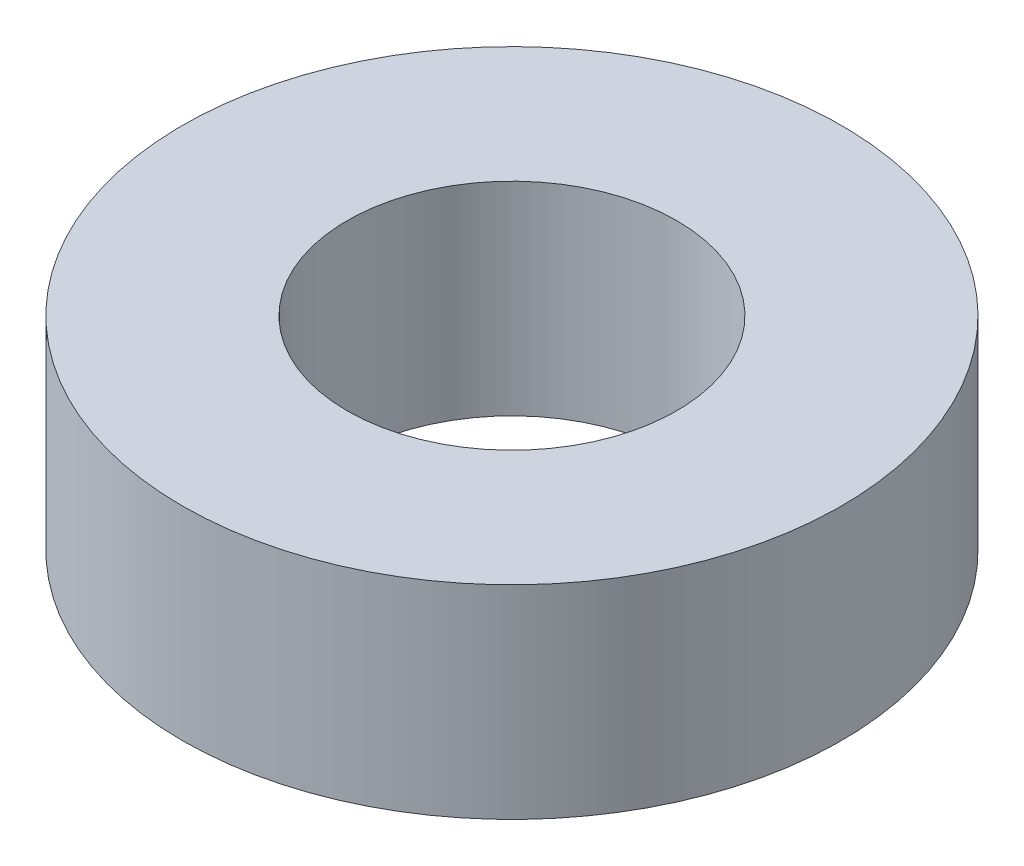
SolidWorks part; units mm, degrees
ref_plane "Front Plane" through (0, 0, 0) normal (0, 0, 1) x (1, 0, 0)
ref_plane "Top Plane" through (0, 0, 0) normal (0, 1, 0) x (1, 0, 0)
ref_plane "Right Plane" through (0, 0, 0) normal (1, 0, 0) x (0, 0, -1)
sketch "Sketch1" plane through (0, 0, 0) normal (0, 1, 0) x (1, 0, 0)
  circle A0 centre (0, 0) radius 3
  circle A1 centre (0, 0) radius 1.5
  dimension "D1" = 3
  dimension "D2" = 1.5
extrude "Boss-Extrude1" add sketch "Sketch1" along normal blind 1.85
